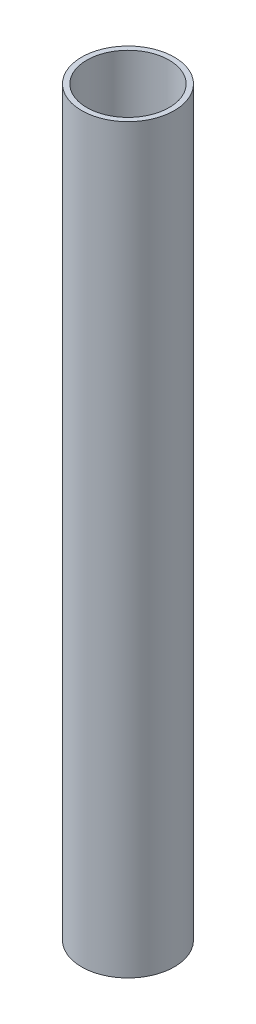
SolidWorks part; units mm, degrees
ref_plane "Front Plane" through (0, 0, 0) normal (0, 0, 1) x (1, 0, 0)
ref_plane "Top Plane" through (0, 0, 0) normal (0, 1, 0) x (1, 0, 0)
ref_plane "Right Plane" through (0, 0, 0) normal (1, 0, 0) x (0, 0, -1)
sketch "Sketch1" plane through (0, 0, 0) normal (0, 1, 0) x (1, 0, 0)
  circle A0 centre (0, 0) radius 6.35
  circle A1 centre (0, 0) radius 5.6388
  dimension "D1" = 12.7
  dimension "D2" = 11.2776
extrude "Boss-Extrude1" add sketch "Sketch1" along normal blind 101.6
